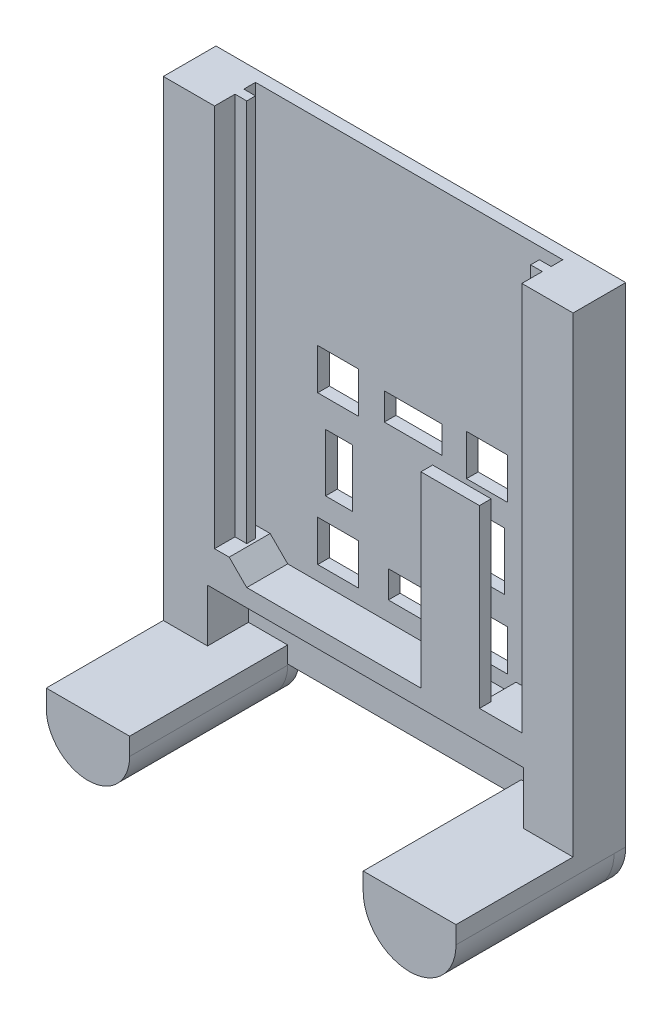
SolidWorks part; units mm, degrees
ref_plane "Front Plane" through (0, 0, 0) normal (0, 0, 1) x (1, 0, 0)
ref_plane "Top Plane" through (0, 0, 0) normal (0, 1, 0) x (1, 0, 0)
ref_plane "Right Plane" through (0, 0, 0) normal (1, 0, 0) x (0, 0, -1)
sketch "Sketch2" plane through (0, 0, 0) normal (0, 0, 1) x (1, 0, 0)
  line L1 (70, 0) -> (70, 71.493)
  line L3 (0, 71.493) -> (0, 0)
  line L4 (8.75, 71.493) -> (8.75, 5.993)
  line L5 (8.75, 5.993) -> (11.25, 5.993)
  line L6 (11.25, 5.993) -> (14.25, 2.993)
  line L7 (14.25, 2.993) -> (51.3651, 2.993)
  line L8 (51.3651, 2.993) -> (53.25, 4.993)
  line L9 (53.25, 4.993) -> (61.25, 4.993)
  line L10 (61.25, 4.993) -> (61.25, 71.493)
  line L11 (0, 71.493) -> (8.75, 71.493)
  line L12 (61.25, 71.493) -> (70, 71.493)
  line L13 (0, 0) -> (0, -12)
  line L15 (14.2403, -12) -> (14.2403, -9)
  line L16 (14.2403, -9) -> (7.5511, -9)
  line L17 (7.5511, -9) -> (7.5511, 0)
  line L18 (7.5511, 0) -> (61.5511, 0)
  line L19 (61.5511, 0) -> (61.5511, -9)
  line L20 (61.5511, -9) -> (54.1431, -9)
  line L21 (54.1431, -9) -> (54.1431, -12)
  line L23 (70, -12) -> (70, 0)
  arc A0 (0, -12) -> (14.2403, -12) centre (7.1201, -12) ccw
  arc A1 (54.1431, -12) -> (70, -12) centre (62.0715, -12) ccw
  dimension "D1" = 70
  dimension "D2" = 68.5
  dimension "D3" = 3
  dimension "D4" = 2.5
  dimension "D5" = 8.75
  dimension "D6" = 8.75
  dimension "D7" = 8
  dimension "D8" = 68.5
  dimension "D9" = 54
  dimension "D10" = 9
  dimension "D11" = 9
  dimension "D12" = 2
extrude "Boss-Extrude1" add sketch "Sketch2" along normal blind 7
sketch "Sketch3" plane through (8.75, 0, 0) normal (1, 0, 0) x (0, 0, -1)
  line L1 (-7, 71.493) -> (0, 71.493) construction
  line L2 (-7, 5.993) -> (0, 5.993) construction
  line L3 (-3.5, 5.993) -> (-2, 5.993)
  line L4 (-2, 5.993) -> (-2, 71.493)
  line L6 (-3.5, 71.493) -> (-2, 71.493)
  line L7 (-3.5, 71.493) -> (-3.5, 5.993)
  line L8 (-3.5, 5.993) -> (-2, 5.993)
  dimension "D1" = 2
  dimension "D2" = 1.5
extrude "Boss-Extrude2" add sketch "Sketch3" along normal blind 2 contours L8 L7 L6 L4
sketch "Sketch4" plane through (61.25, 0, 0) normal (-1, 0, 0) x (0, 0, 1)
  line L0 (2, 71.493) -> (3.5, 71.493)
  line L1 (7, 71.493) -> (0, 71.493) construction
  line L2 (3.5, 71.493) -> (3.5, 4.993)
  line L3 (7, 4.993) -> (0, 4.993) construction
  line L4 (3.5, 4.993) -> (2, 4.993)
  line L5 (2, 4.993) -> (2, 71.493)
  dimension "D1" = 2
  dimension "D2" = 1.5
extrude "Boss-Extrude3" add sketch "Sketch4" along normal blind 2
sketch "Sketch7" plane through (0, 0, 7) normal (0, 0, 1) x (1, 0, 0)
  line L0 (44.0075, 1.5538) -> (54.0075, 1.5538)
  line L2 (54.0075, 1.5538) -> (54.0075, 35)
  line L3 (54.0075, 35) -> (44.0075, 35)
  line L4 (44.0075, 35) -> (44.0075, 1.5538)
  dimension "D1" = 10
extrude "Boss-Extrude6" add sketch "Sketch7" against normal blind 2
sketch "Sketch8" plane through (0, 0, 0) normal (0, 0, -1) x (-1, 0, 0)
  line L1 (-70, 71.493) -> (0, 71.493)
  line L2 (-70, 71.493) -> (-70, -12)
  line L4 (0, 71.493) -> (0, -11.8213)
  line L5 (-70, -12) -> (-70, 71.493) construction
  line L6 (0, 71.493) -> (0, -12) construction
  line L7 (-54.1431, -11.8213) -> (-14.2403, -11.8213)
  line L8 (-54.1431, -9) -> (-54.1431, -12) construction
  line L9 (-14.2403, -12) -> (-14.2403, -9) construction
  line L10 (-70, -12) -> (-70, 71.493) construction
  arc A0 (-70, -12) -> (-54.1431, -12) centre (-62.0715, -12) ccw construction
  arc A1 (-70, -12) -> (-54.1431, -11.8213) centre (-62.0705, -12) ccw
  arc A2 (-14.2403, -11.8213) -> (0, -11.8213) centre (-7.1201, -11.9978) ccw
extrude "Boss-Extrude7" add sketch "Sketch8" along normal blind 2
sketch "Sketch14" plane through (0, 0, 7) normal (0, 0, 1) x (1, 0, 0)
  line L2 (14.2403, -12) -> (14.2403, -9)
  line L3 (14.2403, -9) -> (0, -9)
  line L4 (0, 71.493) -> (0, -12) construction
  line L5 (0, -9) -> (0, -12)
  line L6 (54.1431, -12) -> (54.1431, -9)
  line L7 (54.1431, -9) -> (70, -9)
  line L8 (70, -12) -> (70, 71.493) construction
  line L9 (70, -9) -> (70, -12)
  arc A0 (0, -12) -> (14.2403, -12) centre (7.1201, -12) ccw
  arc A1 (54.1431, -12) -> (70, -12) centre (62.0715, -12) ccw
extrude "Boss-Extrude8" add sketch "Sketch14" along normal blind 20
sketch "Sketch15" plane through (0, 0, -2) normal (0, 0, -1) x (-1, 0, 0)
  line L0 (-35.5844, 71.493) -> (-35.5844, -17.9749) construction
  line L1 (0, 71.493) -> (-70, 71.493) construction
  line L2 (-51.7944, 12.4634) -> (-44.7944, 12.4634)
  line L3 (-51.7944, 37.8738) -> (-44.7944, 37.8738)
  line L4 (-51.7944, 37.8738) -> (-51.7944, 30.8738)
  line L5 (-51.7944, 30.8738) -> (-44.7944, 30.8738)
  line L6 (-44.7944, 37.8738) -> (-44.7944, 30.8738)
  line L7 (-51.7944, 12.4634) -> (-51.7944, 5.4634)
  line L8 (-51.7944, 5.4634) -> (-44.7944, 5.4634)
  line L9 (-44.7944, 12.4634) -> (-44.7944, 5.4634)
  line L10 (-26.3744, 12.4634) -> (-26.3744, 5.4634)
  line L11 (-19.3744, 5.4634) -> (-26.3744, 5.4634)
  line L12 (-19.3744, 12.4634) -> (-19.3744, 5.4634)
  line L13 (-26.3744, 37.8738) -> (-26.3744, 30.8738)
  line L14 (-19.3744, 30.8738) -> (-26.3744, 30.8738)
  line L15 (-19.3744, 37.8738) -> (-19.3744, 30.8738)
  line L16 (-19.3744, 37.8738) -> (-26.3744, 37.8738)
  line L17 (-19.3744, 12.4634) -> (-26.3744, 12.4634)
  dimension "D1" = 7
  dimension "D2" = 7
  dimension "D3" = 32.4104
  dimension "D4" = 16.21
  dimension "D5" = 16.21
  dimension "D6" = 7
  dimension "D7" = 7
extrude "Cut-Extrude4" cut sketch "Sketch15" against normal blind 2
sketch "Sketch16" plane through (0, 0, -2) normal (0, 0, -1) x (-1, 0, 0)
  line L0 (-46.6907, 16.9785) -> (-46.6907, 26.8255)
  line L1 (-40.5959, 36.8593) -> (-30.7489, 36.8593)
  line L2 (-40.5959, 36.8593) -> (-40.5959, 32.2254)
  line L3 (-40.5959, 32.2254) -> (-30.7489, 32.2254)
  line L4 (-30.7489, 36.8593) -> (-30.7489, 32.2254)
  line L5 (-51.3246, 16.9785) -> (-46.6907, 16.9785)
  line L6 (-51.3246, 16.9785) -> (-51.3246, 26.8255)
  line L7 (-51.3246, 26.8255) -> (-46.6907, 26.8255)
  line L8 (-31.4438, 10.8836) -> (-41.2908, 10.8836)
  line L9 (-31.4438, 6.2498) -> (-31.4438, 10.8836)
  line L10 (-31.4438, 6.2498) -> (-41.2908, 6.2498)
  line L11 (-41.2908, 6.2498) -> (-41.2908, 10.8836)
  line L12 (-25.3489, 26.1305) -> (-25.3489, 16.2836)
  line L13 (-20.7151, 26.1305) -> (-25.3489, 26.1305)
  line L14 (-20.7151, 26.1305) -> (-20.7151, 16.2836)
  line L15 (-20.7151, 16.2836) -> (-25.3489, 16.2836)
  point P19 (-36.0198, 21.5545)
  dimension "D1" = 4
extrude "Cut-Extrude5" cut sketch "Sketch16" against normal blind 2
